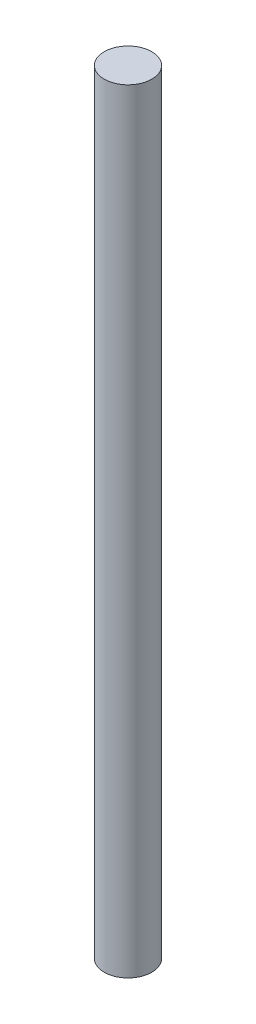
SolidWorks part; units mm, degrees
material "6061 Alloy"
ref_plane "Front Plane" through (0, 0, 0) normal (0, 0, 1) x (1, 0, 0)
ref_plane "Top Plane" through (0, 0, 0) normal (0, 1, 0) x (1, 0, 0)
ref_plane "Right Plane" through (0, 0, 0) normal (1, 0, 0) x (0, 0, -1)
sketch "Sketch1" plane through (0, 0, 0) normal (0, 0, 1) x (1, 0, 0)
  line L0 (0, 0) -> (0, 25.5113) construction
  line L1 (0, -32.5) -> (2, -32.5)
  line L2 (0, -32.5) -> (0, 32.5)
  line L3 (0, 32.5) -> (2, 32.5)
  line L4 (2, -32.5) -> (2, 32.5)
  dimension "D1" = 4
  dimension "D2" = 65
revolve "Revolve1" add sketch "Sketch1" angle 360 about L0
